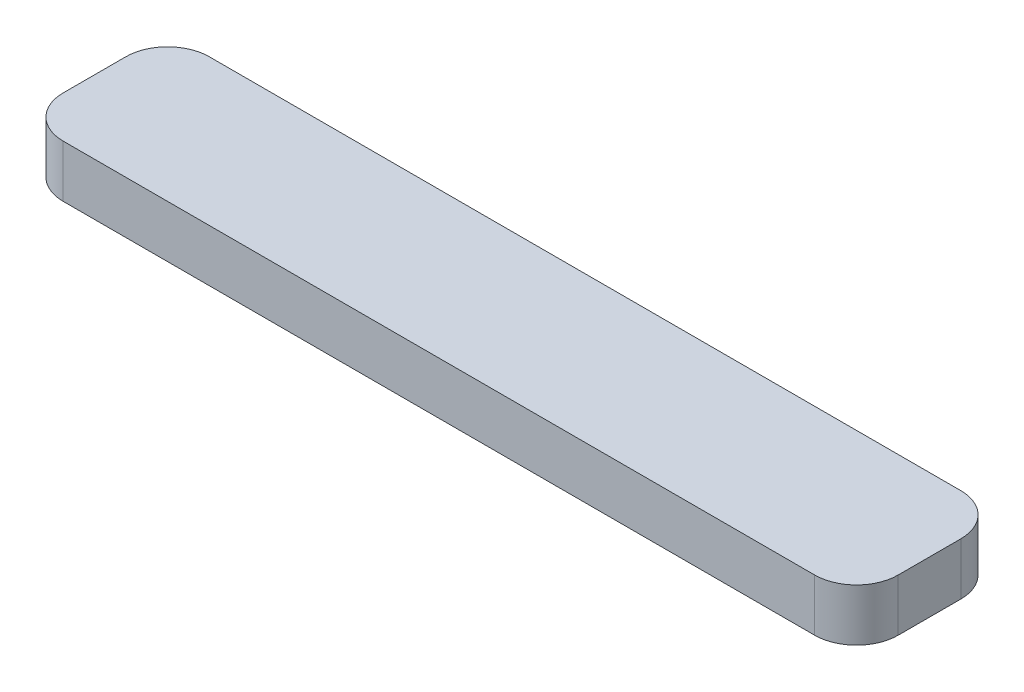
SolidWorks part; units mm, degrees
ref_plane "Front Plane" through (0, 0, 0) normal (0, 0, 1) x (1, 0, 0)
ref_plane "Top Plane" through (0, 0, 0) normal (0, 1, 0) x (1, 0, 0)
ref_plane "Right Plane" through (0, 0, 0) normal (1, 0, 0) x (0, 0, -1)
sketch "Sketch1" plane through (0, 0, 0) normal (0, 1, 0) x (1, 0, 0)
  line L1 (25.4, 4.445) -> (-25.4, 4.445)
  line L2 (25.4, 4.445) -> (25.4, -4.445)
  line L3 (25.4, -4.445) -> (-25.4, -4.445)
  line L4 (-25.4, 4.445) -> (-25.4, -4.445)
  line L5 (25.4, 4.445) -> (-25.4, -4.445) construction
  line L6 (25.4, -4.445) -> (-25.4, 4.445) construction
  point P0 (0, 0)
  dimension "D1" = 8.89
  dimension "D2" = 50.8
extrude "Boss-Extrude1" add sketch "Sketch1" along normal mid plane 3.175
fillet "Fillet1" radius 2.54 4 edges at (-25.4, 0, -4.445) (-25.4, 0, 4.445) (25.4, 0, 4.445) (25.4, 0, -4.445)
